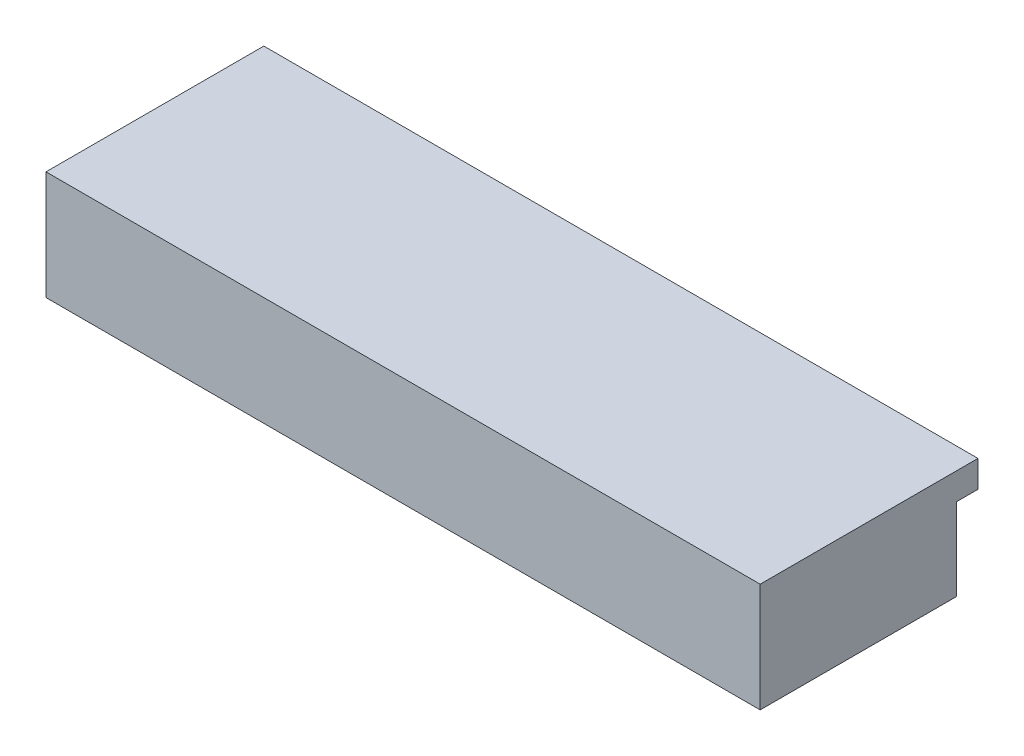
SolidWorks part; units mm, degrees
ref_plane "Plan de face" through (0, 0, 0) normal (0, 0, 1) x (1, 0, 0)
ref_plane "Plan de dessus" through (0, 0, 0) normal (0, 1, 0) x (1, 0, 0)
ref_plane "Plan de droite" through (0, 0, 0) normal (1, 0, 0) x (0, 0, -1)
sketch "Esquisse3" plane through (0, 0, 0) normal (0, 0, 1) x (1, 0, 0)
  line L4 (238, 25) -> (-162, 25)
  line L5 (-162, 25) -> (-162, -15)
  line L6 (-162, -15) -> (238, -15)
  line L7 (238, -15) -> (238, 25)
  line L8 (238, 25) -> (-162, 25)
  line L9 (-162, 25) -> (-162, -15)
  line L10 (-162, -15) -> (238, -15)
  line L11 (238, -15) -> (238, 25)
  dimension "D1" = 0
extrude "Extrusion1" add sketch "Esquisse3" along normal blind 110
sketch "Esquisse8" plane through (0, 25, 0) normal (0, 1, 0) x (1, 0, 0)
  line L0 (-162, -110) -> (-162, 0) construction
  line L1 (238, -110) -> (-162, -110)
  line L2 (238, -110) -> (238, 12)
  line L3 (238, 12) -> (-162, 12)
  line L4 (-162, -110) -> (-162, 12)
  line L5 (238, 0) -> (-162, 0) construction
  dimension "D1" = 12
extrude "Extrusion3" add sketch "Esquisse8" along normal blind 15
sketch "Esquisse9" plane through (0, 0, 0) normal (0, 0, -1) x (-1, 0, 0)
  line L0 (-35.5, 10.75) -> (-57.5, 10.75) construction
  line L1 (-57.5, 9.75) -> (-57.5, 0.25) construction
  line L2 (-57.5, -0.75) -> (-35.5, -0.75) construction
  line L3 (-35.5, 0.25) -> (-35.5, 9.75) construction
  line L4 (-118, -6) -> (112, -6)
  line L5 (112, -6) -> (112, 16)
  line L6 (112, 16) -> (-118, 16)
  line L7 (-118, 16) -> (-118, -6)
  line L8 (-118, -6) -> (112, -6)
  line L9 (112, -6) -> (112, 16)
  line L10 (112, 16) -> (-118, 16)
  line L11 (-118, 16) -> (-118, -6)
  line L12 (49.5, 2.5) -> (49.5, 9.5) construction
  line L13 (16, 1.5) -> (49.5, 1.5) construction
  line L14 (16, 9.5) -> (16, 2.5) construction
  line L15 (49.5, 10.5) -> (16, 10.5) construction
  line L16 (-35.5, 10.75) -> (-57.5, 10.75)
  line L17 (-57.5, 9.75) -> (-57.5, 0.25)
  line L18 (-57.5, -0.75) -> (-35.5, -0.75)
  line L19 (-35.5, 0.25) -> (-35.5, 9.75)
  line L20 (49.5, 2.5) -> (49.5, 9.5)
  line L21 (16, 1.5) -> (49.5, 1.5)
  line L22 (16, 9.5) -> (16, 2.5)
  line L23 (49.5, 10.5) -> (16, 10.5)
  dimension "D1" = 0
sketch "Esquisse11" plane through (0, -15, 0) normal (0, -1, 0) x (1, 0, 0)
  line L4 (-162, 0) -> (238, 0)
  line L5 (238, 0) -> (238, 110)
  line L6 (238, 110) -> (-162, 110)
  line L7 (-162, 110) -> (-162, 0)
  line L8 (-162, 0) -> (238, 0)
  line L9 (238, 0) -> (238, 110)
  line L10 (238, 110) -> (-162, 110)
  line L11 (-162, 110) -> (-162, 0)
  dimension "D1" = 0
extrude "Extrusion5" add sketch "Esquisse11" along normal blind 6
sketch "Esquisse10" plane through (0, 0, 0) normal (0, 0, -1) x (-1, 0, 0)
  line L0 (-35.5, 0.25) -> (-35.5, 9.75) construction
  line L1 (-31.5, -3) -> (-61.5, -3)
  line L2 (-30.5, -2) -> (-30.5, 12)
  line L3 (-31.5, 13) -> (-61.5, 13)
  line L4 (-62.5, -2) -> (-62.5, 12)
  line L5 (-57.5, -0.75) -> (-35.5, -0.75) construction
  line L6 (16, 1.5) -> (49.5, 1.5) construction
  line L7 (51.75, 0) -> (12.75, 0)
  line L8 (52.75, 1) -> (52.75, 11)
  line L9 (51.75, 12) -> (12.75, 12)
  line L10 (11.75, 1) -> (11.75, 11)
  line L12 (16, 9.5) -> (16, 2.5) construction
  line L14 (59.5, -8) -> (59.5, -19)
  line L15 (70.25, -6) -> (61.5, -6)
  line L16 (-83, 19) -> (70.25, 19)
  line L18 (57.5, -21) -> (-68.5, -21)
  line L19 (-70.5, -19) -> (-70.5, -8)
  line L20 (-72.5, -6) -> (-83, -6)
  arc A0 (70.25, -6) -> (70.25, 19) centre (70.25, 6.5) ccw
  arc A1 (-83, 19) -> (-83, -6) centre (-83, 6.5) ccw
  arc A2 (59.5, -8) -> (61.5, -6) centre (61.5, -8) cw
  arc A3 (59.5, -19) -> (57.5, -21) centre (57.5, -19) cw
  arc A4 (-68.5, -21) -> (-70.5, -19) centre (-68.5, -19) cw
  arc A5 (-72.5, -6) -> (-70.5, -8) centre (-72.5, -8) cw
  arc A6 (51.75, 0) -> (52.75, 1) centre (51.75, 1) ccw
  arc A7 (51.75, 12) -> (52.75, 11) centre (51.75, 11) cw
  arc A8 (12.75, 12) -> (11.75, 11) centre (12.75, 11) ccw
  arc A9 (12.75, 0) -> (11.75, 1) centre (12.75, 1) cw
  arc A10 (-31.5, -3) -> (-30.5, -2) centre (-31.5, -2) ccw
  arc A11 (-30.5, 12) -> (-31.5, 13) centre (-31.5, 12) ccw
  arc A12 (-61.5, 13) -> (-62.5, 12) centre (-61.5, 12) ccw
  arc A13 (-61.5, -3) -> (-62.5, -2) centre (-61.5, -2) cw
  circle A14 centre (-86.5, 6.5) radius 1
  circle A15 centre (-20.5, 6.5) radius 1
  circle A16 centre (72.75, 6.5) radius 1
  point P30 (59.5, -21)
  point P33 (-70.5, -21)
  point P38 (52.75, 0)
  point P43 (11.75, 12)
  point P46 (11.75, 0)
  point P49 (-30.5, -3)
  point P54 (-62.5, 13)
  point P57 (-62.5, -3)
  dimension "D9" = 25
  dimension "D10" = 12.5
  dimension "D16" = 2
  dimension "D17" = 1
  dimension "D18" = 2
  dimension "D20" = 2
  dimension "D21" = 2
  dimension "D1" = 32
  dimension "D2" = 16
  dimension "D3" = 5
  dimension "D4" = 2.25
  dimension "D5" = 12
  dimension "D6" = 41
  dimension "D7" = 1.5
  dimension "D8" = 4.25
  dimension "D11" = 17.5
  dimension "D12" = 7
  dimension "D13" = 130
  dimension "D14" = 8
  dimension "D15" = 40
  dimension "D19" = 24
  dimension "D22" = 10
  dimension "D23" = 20
extrude "Extrusion4" cut sketch "Esquisse10" against normal blind 1.5
sketch "Esquisse12" plane through (0, 0, 0) normal (0, 0, -1) x (-1, 0, 0)
  line L4 (-30.5, -2) -> (-30.5, 12)
  line L5 (-31.5, 13) -> (-61.5, 13)
  line L6 (-62.5, 12) -> (-62.5, -2)
  line L7 (-61.5, -3) -> (-31.5, -3)
  line L8 (-30.5, -2) -> (-30.5, 12)
  line L9 (-31.5, 13) -> (-61.5, 13)
  line L10 (-62.5, 12) -> (-62.5, -2)
  line L11 (-61.5, -3) -> (-31.5, -3)
  line L14 (52.75, 1) -> (52.75, 11)
  line L15 (51.75, 12) -> (12.75, 12)
  line L16 (11.75, 11) -> (11.75, 1)
  line L17 (12.75, 0) -> (51.75, 0)
  line L18 (52.75, 1) -> (52.75, 11)
  line L19 (51.75, 12) -> (12.75, 12)
  line L20 (11.75, 11) -> (11.75, 1)
  line L21 (12.75, 0) -> (51.75, 0)
  circle A2 centre (-86.5, 6.5) radius 1
  circle A3 centre (-20.5, 6.5) radius 1
  arc A4 (-31.5, -3) -> (-30.5, -2) centre (-31.5, -2) ccw
  arc A5 (-30.5, 12) -> (-31.5, 13) centre (-31.5, 12) ccw
  arc A6 (-61.5, 13) -> (-62.5, 12) centre (-61.5, 12) ccw
  arc A7 (-62.5, -2) -> (-61.5, -3) centre (-61.5, -2) ccw
  arc A8 (-31.5, -3) -> (-30.5, -2) centre (-31.5, -2) ccw
  arc A9 (-30.5, 12) -> (-31.5, 13) centre (-31.5, 12) ccw
  arc A10 (-61.5, 13) -> (-62.5, 12) centre (-61.5, 12) ccw
  arc A11 (-62.5, -2) -> (-61.5, -3) centre (-61.5, -2) ccw
  circle A12 centre (-20.5, 6.5) radius 1
  circle A13 centre (72.75, 6.5) radius 1
  circle A14 centre (72.75, 6.5) radius 1
  arc A18 (51.75, 0) -> (52.75, 1) centre (51.75, 1) ccw
  arc A19 (52.75, 11) -> (51.75, 12) centre (51.75, 11) ccw
  arc A20 (12.75, 12) -> (11.75, 11) centre (12.75, 11) ccw
  arc A21 (11.75, 1) -> (12.75, 0) centre (12.75, 1) ccw
  arc A22 (51.75, 0) -> (52.75, 1) centre (51.75, 1) ccw
  arc A23 (52.75, 11) -> (51.75, 12) centre (51.75, 11) ccw
  arc A24 (12.75, 12) -> (11.75, 11) centre (12.75, 11) ccw
  arc A25 (11.75, 1) -> (12.75, 0) centre (12.75, 1) ccw
  dimension "D2" = 2
  dimension "D1" = 0
  dimension "D3" = 0
  dimension "D4" = 0
  dimension "D5" = 0
extrude "Extrusion6" cut sketch "Esquisse12" against normal blind 20
